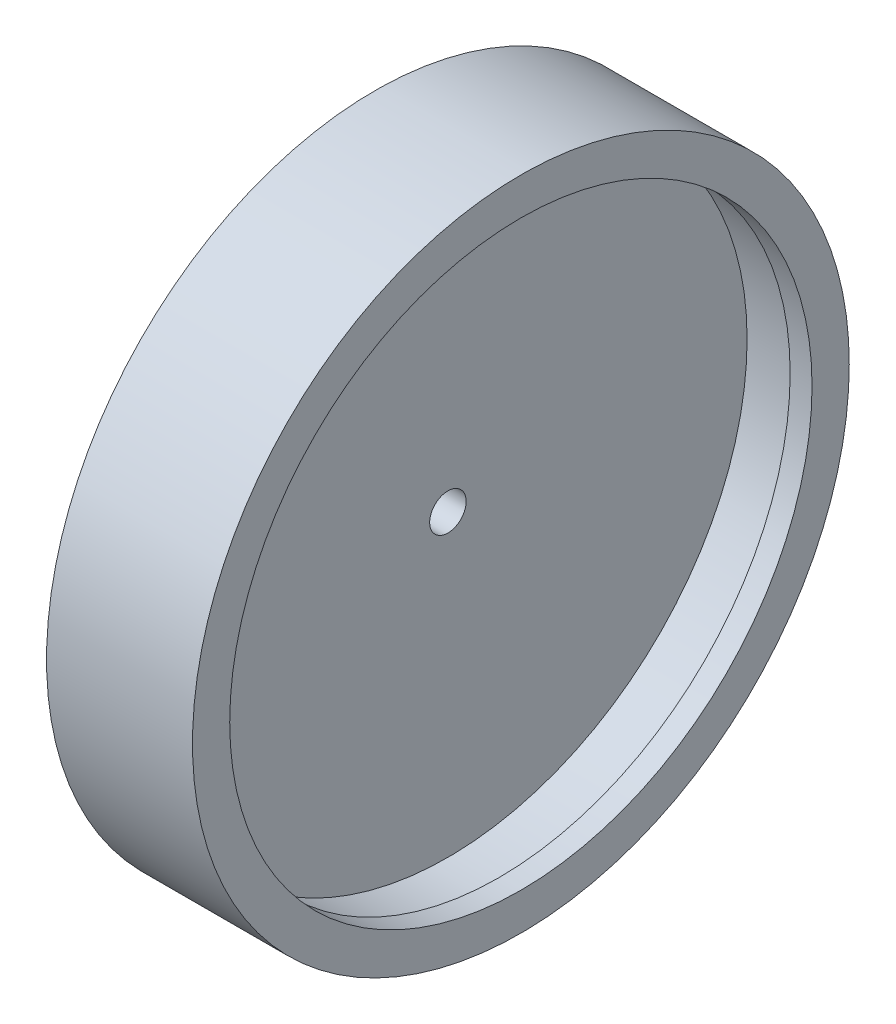
SolidWorks part; units mm, degrees
ref_plane "Alzado" through (0, 0, 0) normal (0, 0, 1) x (1, 0, 0)
ref_plane "Planta" through (0, 0, 0) normal (0, 1, 0) x (1, 0, 0)
ref_plane "Vista lateral" through (0, 0, 0) normal (1, 0, 0) x (0, 0, -1)
sketch "Croquis2" plane through (0, 0, 0) normal (1, 0, 0) x (0, 0, -1)
  circle A0 centre (-3.3341, 2.4392) radius 41
  circle A1 centre (-3.3341, 2.4392) radius 45
  dimension "D1" = 82
  dimension "D2" = 90
extrude "Saliente-Extruir1" add sketch "Croquis2" along normal blind 10 contours A1 A0
sketch "Croquis3" plane through (0, 0, 0) normal (1, 0, 0) x (0, 0, -1)
  circle A0 centre (-3.3341, 2.4392) radius 45
extrude "Saliente-Extruir2" add sketch "Croquis3" against normal blind 10
sketch "Croquis4" plane through (10, 0, 0) normal (1, 0, 0) x (0, 0, -1)
  circle A0 centre (-3.3341, 2.4392) radius 45
  circle A1 centre (-3.3341, 2.4392) radius 39.9
  dimension "D1" = 79.8
extrude "Saliente-Extruir3" add sketch "Croquis4" against normal blind 3
sketch "Croquis5" plane through (0, 0, 0) normal (1, 0, 0) x (0, 0, -1)
  circle A1 centre (-3.3341, 2.4392) radius 2.5
  dimension "D1" = 5
extrude "Cortar-Extruir1" cut sketch "Croquis5" against normal blind 10
